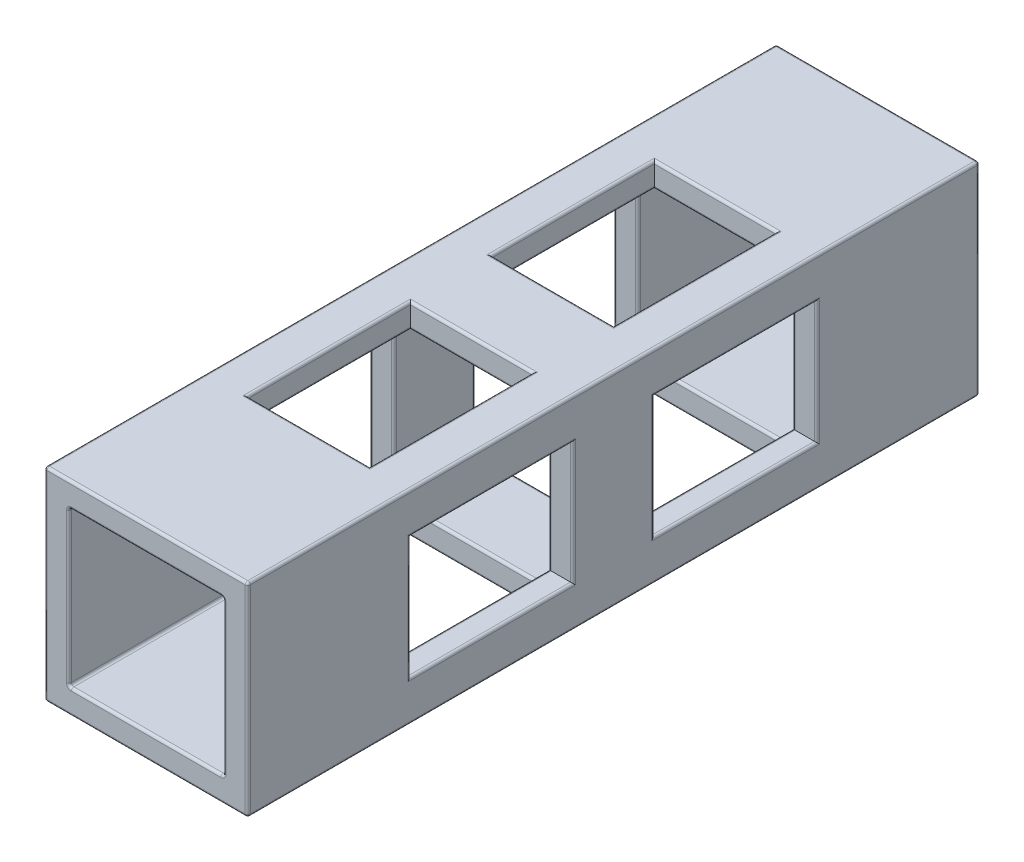
SolidWorks part; units mm, degrees
ref_plane "Front Plane" through (0, 0, 0) normal (0, 0, 1) x (1, 0, 0)
ref_plane "Top Plane" through (0, 0, 0) normal (0, 1, 0) x (1, 0, 0)
ref_plane "Right Plane" through (0, 0, 0) normal (1, 0, 0) x (0, 0, -1)
sketch "Sketch1" plane through (0, 0, 0) normal (0, 0, 1) x (1, 0, 0)
  line L5 (-22.2643, 19.094) -> (9.4857, 19.094)
  line L6 (-22.2643, 19.094) -> (-22.2643, -12.656)
  line L7 (-22.2643, -12.656) -> (9.4857, -12.656)
  line L8 (9.4857, 19.094) -> (9.4857, -12.656)
  dimension "D1" = 31.75
  dimension "D2" = 31.75
extrude "Boss-Extrude1" add sketch "Sketch1" along normal blind 114.3
sketch "Sketch3" plane through (0, 0, 114.3) normal (0, 0, 1) x (1, 0, 0)
  line L0 (-22.2643, 19.094) -> (-22.2643, -12.656) construction
  line L1 (-18.4543, 15.284) -> (5.6757, 15.284)
  line L2 (-18.4543, 15.284) -> (-18.4543, -8.846)
  line L3 (-18.4543, -8.846) -> (5.6757, -8.846)
  line L4 (5.6757, 15.284) -> (5.6757, -8.846)
  line L5 (-22.2643, -12.656) -> (9.4857, -12.656) construction
  line L6 (9.4857, -12.656) -> (9.4857, 19.094) construction
  line L7 (9.4857, 19.094) -> (-22.2643, 19.094) construction
  dimension "D1" = 3.81
  dimension "D2" = 3.81
  dimension "D3" = 3.81
  dimension "D4" = 3.81
extrude "Cut-Extrude1" cut sketch "Sketch3" against normal blind 114.3 contours L2 L1 L4 L3
sketch "Sketch4" plane through (0, 19.094, 0) normal (0, 1, 0) x (1, 0, 0)
  line L0 (9.4857, 0) -> (-22.2643, 0) construction
  line L1 (-15.9143, -25.4) -> (3.1357, -25.4)
  line L4 (3.1357, -25.4) -> (3.1357, -50.8)
  line L13 (-6.3893, 0) -> (-6.3893, -122.3336) construction
  line L14 (9.4857, -114.3) -> (9.4857, 0) construction
  line L20 (-22.2643, -57.15) -> (13.4769, -57.15) construction
  line L22 (-22.2643, -114.3) -> (-22.2643, 0) construction
  line L23 (-15.9143, -25.4) -> (-15.9143, -50.8)
  line L25 (-15.9143, -38.1) -> (3.1357, -38.1) construction
  line L26 (-15.9143, -50.8) -> (3.1357, -50.8)
  line L27 (-15.9143, -25.4) -> (3.1357, -25.4)
  line L28 (-15.9143, -50.8) -> (3.1357, -50.8)
  line L29 (-15.9143, -63.5) -> (3.1357, -63.5)
  line L30 (-15.9143, -88.9) -> (3.1357, -88.9)
  line L31 (-15.9143, -88.9) -> (-15.9143, -63.5)
  line L32 (3.1357, -88.9) -> (3.1357, -63.5)
  point P6 (-144.9504, -35.8613)
  dimension "D1" = 25.4
  dimension "D2" = 50.8
  dimension "D3" = 6.35
sketch "Sketch10" plane through (9.4857, 0, 0) normal (1, 0, 0) x (0, 0, -1)
  line L0 (-88.9, 12.744) -> (-63.5, 12.744)
  line L1 (-88.9, 19.094) -> (-63.5, 19.094) construction
  line L2 (-88.9, 12.744) -> (-88.9, -6.306)
  line L3 (-114.3, -12.656) -> (-114.3, 19.094) construction
  line L4 (-57.15, -12.656) -> (-57.15, 46.132) construction
  line L5 (-114.3, -12.656) -> (0, -12.656) construction
  line L6 (-114.3, 3.219) -> (5.0012, 3.219) construction
  line L7 (-63.5, 12.744) -> (-63.5, -6.306)
  line L8 (-88.9, -6.306) -> (-63.5, -6.306)
  line L9 (-88.9, 12.744) -> (-63.5, 12.744)
  line L10 (-88.9, -6.306) -> (-63.5, -6.306)
  line L11 (-25.4, -6.306) -> (-50.8, -6.306)
  line L12 (-25.4, 12.744) -> (-50.8, 12.744)
  line L13 (-25.4, -6.306) -> (-50.8, -6.306)
  line L14 (-50.8, 12.744) -> (-50.8, -6.306)
  line L15 (-25.4, 12.744) -> (-25.4, -6.306)
  line L16 (-25.4, 12.744) -> (-50.8, 12.744)
  point P16 (0, 0)
  dimension "D1" = 6.35
  dimension "D2" = 25.4
  dimension "D3" = 50.8
sketch "Sketch13" plane through (0, -12.656, 0) normal (0, -1, 0) x (1, 0, 0)
  line L0 (-15.9143, 88.9) -> (3.1357, 88.9)
  line L1 (3.1357, 88.9) -> (3.1357, 63.5)
  line L2 (3.1357, 63.5) -> (-15.9143, 63.5)
  line L3 (-15.9143, 63.5) -> (-15.9143, 88.9)
  line L4 (9.4857, 57.15) -> (-22.2643, 57.15) construction
  line L5 (-22.2643, 57.15) -> (13.4769, 57.15) construction
  line L6 (9.4857, 114.3) -> (9.4857, -5.0012) construction
  line L7 (-15.9143, 50.8) -> (-15.9143, 25.4)
  line L8 (3.1357, 50.8) -> (-15.9143, 50.8)
  line L9 (3.1357, 25.4) -> (3.1357, 50.8)
  line L10 (-15.9143, 25.4) -> (3.1357, 25.4)
sketch "Sketch14" plane through (-22.2643, 0, 0) normal (-1, 0, 0) x (0, 0, 1)
  line L0 (88.9, 12.744) -> (88.9, -6.306)
  line L1 (88.9, 12.744) -> (63.5, 12.744)
  line L3 (63.5, 12.744) -> (63.5, -6.306)
  line L4 (63.5, -6.306) -> (88.9, -6.306)
  line L5 (57.15, 34.1154) -> (57.15, -18.5433) construction
  line L6 (57.15, -12.656) -> (57.15, 46.132) construction
  line L7 (50.8, -6.306) -> (25.4, -6.306)
  line L8 (50.8, 12.744) -> (50.8, -6.306)
  line L9 (25.4, 12.744) -> (50.8, 12.744)
  line L10 (25.4, 12.744) -> (25.4, -6.306)
extrude "Cut-Extrude4" cut sketch "Sketch4" against normal blind 6.35 contours L30 L32 L29 L31 | L23 L26 L4 L1
extrude "Cut-Extrude5" cut sketch "Sketch10" against normal blind 6.35 contours L2 L8 L7 L0 | L15 L12 L14 L11
extrude "Cut-Extrude6" cut sketch "Sketch13" against normal blind 6.35
extrude "Cut-Extrude7" cut sketch "Sketch14" against normal blind 6.35
fillet "Fillet1/64" radius 0.3969 88 edges at (-6.3893, 15.284, 0) (5.6757, 3.219, 0) (-6.3893, -8.846, 0) (-18.4543, 3.219, 0) (5.6757, 3.219, 114.3) (-6.3893, 15.284, 114.3) (-18.4543, 3.219, 114.3) (-6.3893, -8.846, 114.3) (-22.2643, 3.219, 114.3) (-22.2643, 3.219, 0) (-22.2643, 3.219, 25.4) (-22.2643, -6.306, 38.1) (-22.2643, 3.219, 50.8) (-22.2643, 12.744, 38.1) (-22.2643, -6.306, 76.2) (-22.2643, 3.219, 88.9) (-22.2643, 12.744, 76.2) (-22.2643, 3.219, 63.5) (-22.2643, -12.656, 57.15) (-6.3893, -12.656, 114.3) (-6.3893, -12.656, 0) (-6.3893, -12.656, 25.4) (3.1357, -12.656, 38.1) (-6.3893, -12.656, 50.8) (-15.9143, -12.656, 38.1) (3.1357, -12.656, 76.2) (-6.3893, -12.656, 88.9) (-15.9143, -12.656, 76.2) (-6.3893, -12.656, 63.5) (-6.3893, 19.094, 114.3) (-22.2643, 19.094, 57.15) (-6.3893, 19.094, 0) (3.1357, 19.094, 38.1) (-6.3893, 19.094, 25.4) (-15.9143, 19.094, 38.1) (-6.3893, 19.094, 50.8) (-6.3893, 19.094, 63.5) (-15.9143, 19.094, 76.2) (-6.3893, 19.094, 88.9) (3.1357, 19.094, 76.2) (9.4857, 12.744, 38.1) (9.4857, 3.219, 50.8) (9.4857, -6.306, 38.1) (9.4857, 3.219, 25.4) (9.4857, -12.656, 57.15) (9.4857, 3.219, 114.3) (9.4857, 19.094, 57.15) (9.4857, 3.219, 0) (9.4857, 3.219, 63.5) (9.4857, 12.744, 76.2) (9.4857, 3.219, 88.9) (9.4857, -6.306, 76.2) (5.6757, 3.219, 50.8) (5.6757, 12.744, 38.1) (5.6757, 3.219, 25.4) (5.6757, -6.306, 38.1) (5.6757, 12.744, 76.2) (5.6757, 3.219, 63.5) (5.6757, -6.306, 76.2) (5.6757, 3.219, 88.9) (5.6757, 15.284, 57.15) (-6.3893, 15.284, 25.4) (3.1357, 15.284, 38.1) (-6.3893, 15.284, 50.8) (-15.9143, 15.284, 38.1) (-15.9143, 15.284, 76.2) (-6.3893, 15.284, 63.5) (3.1357, 15.284, 76.2) (-6.3893, 15.284, 88.9) (5.6757, -8.846, 57.15) (-6.3893, -8.846, 25.4) (-15.9143, -8.846, 38.1) (-6.3893, -8.846, 50.8) (3.1357, -8.846, 38.1) (3.1357, -8.846, 76.2) (-6.3893, -8.846, 63.5) (-15.9143, -8.846, 76.2) (-6.3893, -8.846, 88.9) (-18.4543, 15.284, 57.15) (-18.4543, -8.846, 57.15) (-18.4543, 3.219, 25.4) (-18.4543, 12.744, 38.1) (-18.4543, 3.219, 50.8) (-18.4543, -6.306, 38.1) (-18.4543, -6.306, 76.2) (-18.4543, 3.219, 63.5) (-18.4543, 12.744, 76.2) (-18.4543, 3.219, 88.9)
equation "\"0..25in\"=0.311636"
